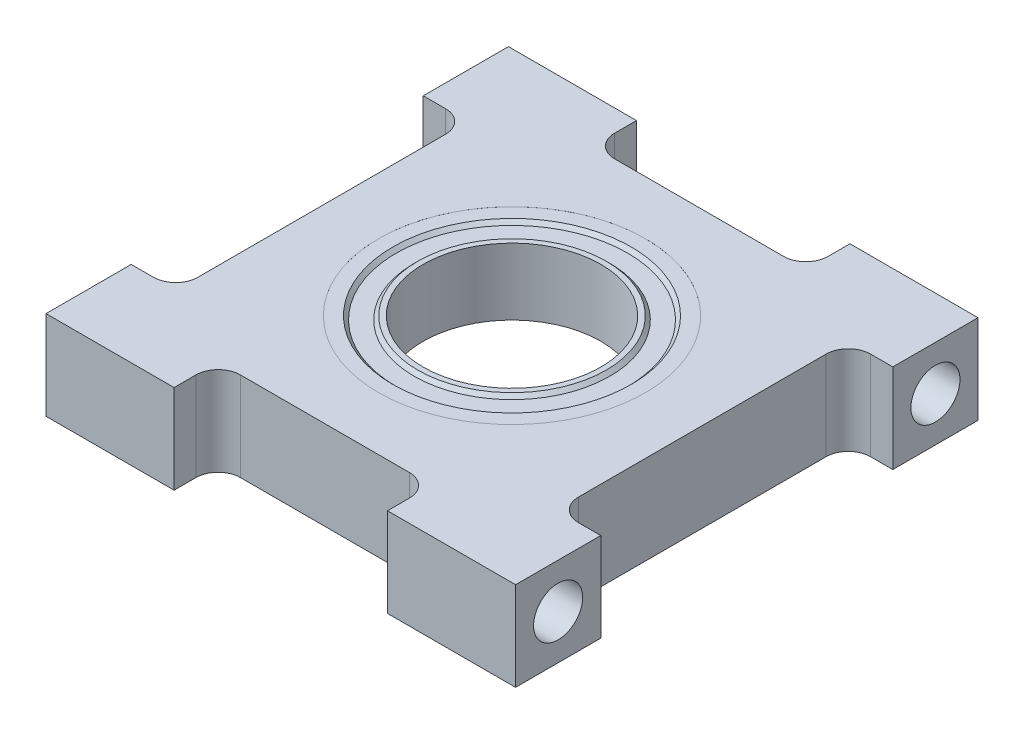
SolidWorks part; units mm, degrees
material "6061 Alloy"
ref_plane "Front Plane" through (0, 0, 0) normal (0, 0, 1) x (1, 0, 0)
ref_plane "Top Plane" through (0, 0, 0) normal (0, 1, 0) x (1, 0, 0)
ref_plane "Right Plane" through (0, 0, 0) normal (1, 0, 0) x (0, 0, -1)
sketch "Sketch1" plane through (0, 0, 0) normal (0, 1, 0) x (1, 0, 0)
  line L0 (-16.764, 0) -> (16.764, 0) construction
  line L1 (-16.764, -16.51) -> (-7.62, -16.51)
  line L2 (-16.764, -16.51) -> (-16.764, -10.4267)
  line L3 (-16.764, 16.51) -> (-7.62, 16.51)
  line L4 (16.764, -16.51) -> (16.764, -10.4267)
  line L5 (-16.764, -16.51) -> (16.764, 16.51) construction
  line L6 (-16.764, 16.51) -> (16.764, -16.51) construction
  line L7 (0, 16.51) -> (0, -16.51) construction
  line L8 (-7.62, -16.51) -> (-7.62, -14.9479)
  line L9 (-6.0325, -13.3604) -> (6.0325, -13.3604)
  line L10 (7.62, -14.9479) -> (7.62, -16.51)
  line L11 (7.62, -16.51) -> (16.764, -16.51)
  line L12 (7.62, 14.9479) -> (7.62, 16.51)
  line L13 (-6.0325, 13.3604) -> (6.0325, 13.3604)
  line L14 (-7.62, 16.51) -> (-7.62, 14.9479)
  line L15 (7.62, 16.51) -> (16.764, 16.51)
  line L16 (-16.764, 10.4267) -> (-15.1765, 10.4267)
  line L17 (-13.589, 8.8392) -> (-13.589, -8.8392)
  line L18 (-15.1765, -10.4267) -> (-16.764, -10.4267)
  line L19 (-16.764, 10.4267) -> (-16.764, 16.51)
  line L20 (15.1765, -10.4267) -> (16.764, -10.4267)
  line L21 (13.589, 8.8392) -> (13.589, -8.8392)
  line L22 (16.764, 10.4267) -> (15.1765, 10.4267)
  line L23 (16.764, 10.4267) -> (16.764, 16.51)
  arc A0 (6.0325, -13.3604) -> (7.62, -14.9479) centre (6.0325, -14.9479) cw
  arc A1 (-7.62, -14.9479) -> (-6.0325, -13.3604) centre (-6.0325, -14.9479) cw
  arc A2 (-7.62, 14.9479) -> (-6.0325, 13.3604) centre (-6.0325, 14.9479) ccw
  arc A3 (6.0325, 13.3604) -> (7.62, 14.9479) centre (6.0325, 14.9479) ccw
  arc A4 (-13.589, -8.8392) -> (-15.1765, -10.4267) centre (-15.1765, -8.8392) cw
  arc A5 (-15.1765, 10.4267) -> (-13.589, 8.8392) centre (-15.1765, 8.8392) cw
  arc A6 (15.1765, 10.4267) -> (13.589, 8.8392) centre (15.1765, 8.8392) ccw
  arc A7 (13.589, -8.8392) -> (15.1765, -10.4267) centre (15.1765, -8.8392) ccw
  circle A8 centre (0, 0) radius 8.89
  point P0 (0, 0)
  dimension "D6" = 1.5875
  dimension "D10" = 1.5875
  dimension "D11" = 17.78
  dimension "D1" = 33.02
  dimension "D2" = 33.528
  dimension "D3" = 15.24
  dimension "D4" = 7.62
  dimension "D5" = 3.1496
  dimension "D7" = 20.8534
  dimension "D8" = 10.4267
  dimension "D9" = 3.175
extrude "Boss-Extrude1" add sketch "Sketch1" along normal blind 6.35
sketch "Sketch2" plane through (0, 6.35, 0) normal (0, 1, 0) x (1, 0, 0)
  circle A0 centre (0, 0) radius 9.525
  dimension "D1" = 19.05
extrude "Cut-Extrude1" cut sketch "Sketch2" against normal blind 4.7625
ref_plane "Plane1" through (0, 1.5875, 0) normal (0, 1, 0) x (-1, 0, 0)
sketch "Sketch3" plane through (0, 1.5875, 0) normal (0, 1, 0) x (-1, 0, 0)
  circle A0 centre (0, 0) radius 9.525
  circle A1 centre (0, 0) radius 8.255
  dimension "D2" = 16.51
  dimension "D1" = 1.27
extrude "Boss-Extrude2" add sketch "Sketch3" along normal blind 4.76
chamfer "Chamfer1" distance 0.254 angle 45 2 edges at (0, 1.5875, 8.255) (0, 6.3475, 8.255)
sketch "Sketch4" plane through (0, 1.5875, 0) normal (0, 1, 0) x (-1, 0, 0)
  circle A0 centre (0, 0) radius 6.35
  circle A1 centre (0, 0) radius 6.985
  dimension "D1" = 12.7
  dimension "D2" = 0.635
extrude "Boss-Extrude3" add sketch "Sketch4" along normal blind 4.76 separate body
chamfer "Chamfer2" distance 0.254 angle 45 2 edges at (0, 1.5875, 6.985) (0, 6.3475, 6.985)
ref_plane "Plane2" through (0, 6.0935, 0) normal (0, 1, 0) x (-1, 0, 0)
sketch "Sketch5" plane through (0, 6.0935, 0) normal (0, 1, 0) x (-1, 0, 0)
  circle A0 centre (0, 0) radius 8.255
  circle A1 centre (0, 0) radius 6.985
  dimension "D1" = 16.51
  dimension "D2" = 13.97
extrude "Boss-Extrude4" add sketch "Sketch5" against normal blind 4.2545
hole_wizard "#6-32 Tapped Hole1" positions "Sketch9" profile "Sketch8" tap size "#6-32" standard "Ansi Inch"
sketch "Sketch9" plane through (-16.764, 0, 0) normal (-1, 0, 0) x (0, 0, 1)
  line L0 (-13.4704, 3.175) -> (13.4704, 3.175) construction
  line L1 (-13.4704, 3.175) -> (0, 16.6454) construction
  line L2 (13.4704, 3.175) -> (0, 16.6454) construction
  line L3 (-16.51, 0) -> (-10.4267, 0) construction
  point P0 (-13.4704, 3.175)
  point P1 (13.4704, 3.175)
  dimension "D1" = 19.05
  dimension "D2" = 19.05
  dimension "D3" = 3.175
sketch "Sketch8" plane through (-16.764, 3.175, -13.4704) normal (0, 1, 0) x (0, 0, 1)
  line L0 (0, 0) -> (0, 8.7629)
  line L1 (0, 8.7629) -> (1.3525, 7.9502)
  line L2 (1.3525, 7.9502) -> (1.3525, 7.0104)
  line L3 (1.3525, 7.0104) -> (1.7526, 7.0104)
  line L4 (1.7526, 7.0104) -> (1.7526, 0)
  line L5 (1.7526, 0) -> (0, 0)
  line L10 (0, 8.7629) -> (-1.3526, 7.9502) construction
  line L11 (0, -6.35) -> (0, 107.95) construction
  dimension "Tap Drill Dia." = 2.7051
  dimension "Tap Drill Depth" = 7.9502
  dimension "Thread Major Dia." = 3.5052
  dimension "Thread Depth" = 7.0104
  dimension "Drill Angle" = 118
mirror "Mirror1" about plane through (0, 0, 0) normal (1, 0, 0) of "#6-32 Tapped Hole1"
